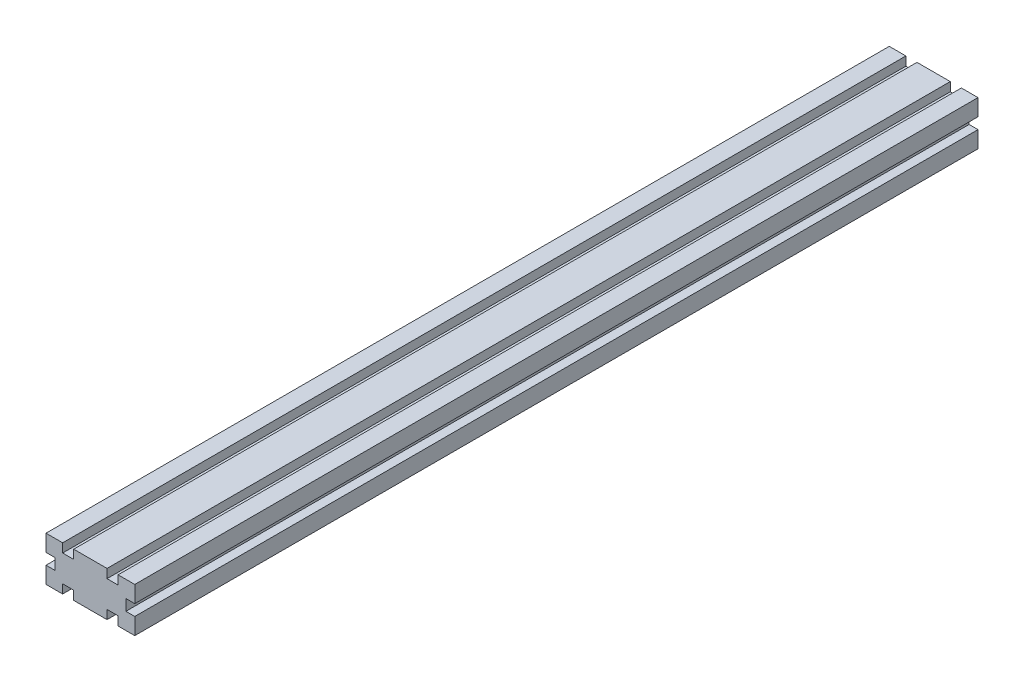
SolidWorks part; units mm, degrees
ref_plane "Plan de face" through (0, 0, 0) normal (0, 0, 1) x (1, 0, 0)
ref_plane "Plan de dessus" through (0, 0, 0) normal (0, 1, 0) x (1, 0, 0)
ref_plane "Plan de droite" through (0, 0, 0) normal (1, 0, 0) x (0, 0, -1)
sketch "Esquisse1" plane through (0, 0, 0) normal (0, 0, 1) x (1, 0, 0)
  line L0 (20, 20) -> (20, 0)
  line L1 (0, 0) -> (40, 0)
  line L2 (0, 0) -> (0, 20)
  line L3 (0, 20) -> (40, 20)
  line L4 (40, 0) -> (40, 20)
  line L5 (20, 0) -> (40, 20)
  line L6 (40, 0) -> (20, 20)
  line L7 (0, 0) -> (20, 20)
  line L8 (20, 0) -> (0, 20)
  line L10 (4, 4) -> (16, 4)
  line L11 (4, 4) -> (4, 16)
  line L12 (4, 16) -> (16, 16)
  line L13 (16, 4) -> (16, 16)
  line L14 (4, 4) -> (16, 16) construction
  line L15 (4, 16) -> (16, 4) construction
  line L16 (24, 4) -> (36, 4)
  line L17 (24, 4) -> (24, 16)
  line L18 (24, 16) -> (36, 16)
  line L19 (36, 4) -> (36, 16)
  line L20 (24, 4) -> (36, 16) construction
  line L21 (24, 16) -> (36, 4) construction
  line L22 (12.5, 0) -> (7.5, 0)
  line L23 (12.5, 0) -> (12.5, 20)
  line L24 (12.5, 20) -> (7.5, 20)
  line L25 (7.5, 0) -> (7.5, 20)
  line L26 (12.5, 0) -> (7.5, 20) construction
  line L27 (12.5, 20) -> (7.5, 0) construction
  line L28 (32.5, 0) -> (27.5, 0)
  line L29 (32.5, 0) -> (32.5, 20)
  line L30 (32.5, 20) -> (27.5, 20)
  line L31 (27.5, 0) -> (27.5, 20)
  line L32 (32.5, 0) -> (27.5, 20) construction
  line L33 (32.5, 20) -> (27.5, 0) construction
  line L34 (0, 7.5) -> (40, 7.5)
  line L35 (0, 7.5) -> (0, 12.5)
  line L36 (0, 12.5) -> (40, 12.5)
  line L37 (40, 7.5) -> (40, 12.5)
  line L38 (0, 7.5) -> (40, 12.5) construction
  line L39 (0, 12.5) -> (40, 7.5) construction
  point P7 (10, 10)
  point P12 (30, 10)
  point P17 (10, 10)
  point P22 (30, 10)
  point P27 (20, 10)
  dimension "D1" = 20
  dimension "D2" = 40
  dimension "D3" = 12
  dimension "D5" = 5
  dimension "D6" = 5
  dimension "D7" = 5
extrude "Boss.-Extru.1" add sketch "Esquisse1" along normal blind 380 contours L12 L25 L3 L8 | L2 L36 L11 L8 | L34 L2 L7 L11 | L1 L25 L10 L7 | L34 L11 L7 | L10 L25 L7 | L11 L36 L8 | L8 L25 L12 | L36 L11 L34 L25 | L25 L7 L8 | L36 L8 L7 | L8 L23 L7 | L7 L34 L8 | L23 L10 L8 | L34 L8 L13 | L34 L13 L8 L0 | L25 L36 L23 L12 | L36 L23 L34 L13 | L23 L7 L12 | L23 L12 L7 L3 | L7 L36 L13 | L13 L36 L0 L7 | L23 L1 L8 L10 | L34 L25 L10 L23 | L36 L13 L34 L0 | L36 L0 L34 L17 | L0 L36 L17 L6 | L18 L31 L3 L6 | L17 L36 L6 | L6 L31 L18 | L36 L17 L34 L31 | L34 L17 L5 | L34 L0 L5 L17 | L1 L31 L16 L5 | L16 L31 L5 | L34 L31 L16 L29 | L29 L16 L6 | L34 L6 L19 | L34 L19 L6 L4 | L29 L1 L6 L16 | L36 L29 L34 L19 | L6 L29 L5 | L5 L34 L6 | L31 L5 L6 | L36 L6 L5 | L5 L36 L19 | L29 L5 L18 | L29 L18 L5 L3 | L19 L36 L4 L5 | L31 L36 L29 L18
